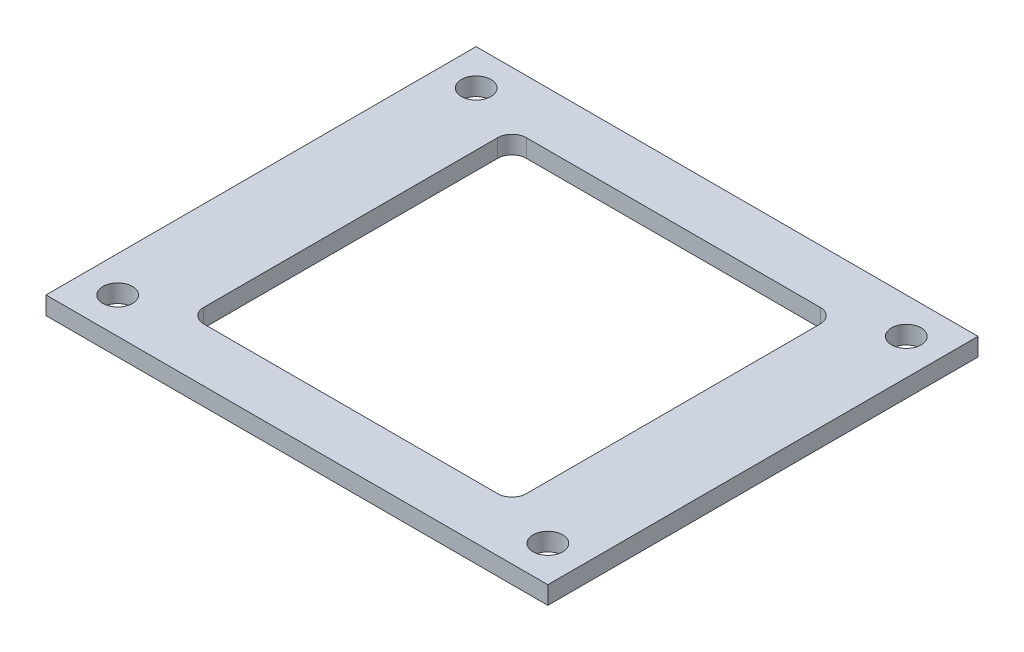
SolidWorks part; units mm, degrees
ref_plane "Front Plane" through (0, 0, 0) normal (0, 0, 1) x (1, 0, 0)
ref_plane "Top Plane" through (0, 0, 0) normal (0, 1, 0) x (1, 0, 0)
ref_plane "Right Plane" through (0, 0, 0) normal (1, 0, 0) x (0, 0, -1)
sketch "Sketch1" plane through (0, 0, 0) normal (0, 1, 0) x (1, 0, 0)
  line L0 (28, 24) -> (-28, 24)
  line L1 (-28, -24) -> (28, -24)
  line L2 (-28, -24) -> (-28, 24)
  line L4 (28, -24) -> (28, 24)
  line L7 (-18, -18) -> (18, -18)
  line L8 (-18, -18) -> (-18, 18)
  line L9 (-18, 18) -> (18, 18)
  line L10 (18, -18) -> (18, 18)
  circle A0 centre (-24, 20) radius 1.65
  circle A1 centre (-24, -20) radius 1.65
  circle A2 centre (24, 20) radius 1.65
  circle A3 centre (24, -20) radius 1.65
  point P0 (0, 0)
  point P5 (0, 0)
  point P19 (28, -24)
  point P20 (0, 0)
  point P22 (0, 0)
  point P23 (0, 0)
  point P24 (0, 0)
  dimension "D5" = 20
  dimension "D6" = 20
  dimension "D7" = 4
  dimension "D8" = 20
  dimension "D9" = 3.3
  dimension "D10" = 3.3
  dimension "D11" = 20
  dimension "D12" = 4
  dimension "D13" = 4
  dimension "D15" = 3.3
  dimension "D16" = 3.3
  dimension "D17" = 4
  dimension "D22" = 24
  dimension "D3" = 36
  dimension "D4" = 36
  dimension "D14" = 56
  dimension "D18" = 18
  dimension "D19" = 18
  dimension "D20" = 24
  dimension "D21" = 28
extrude "Boss-Extrude1" add sketch "Sketch1" along normal blind 2
fillet "Fillet1" radius 1.6 4 edges at (-18, 1, 18) (18, 1, 18) (18, 1, -18) (-18, 1, -18)
